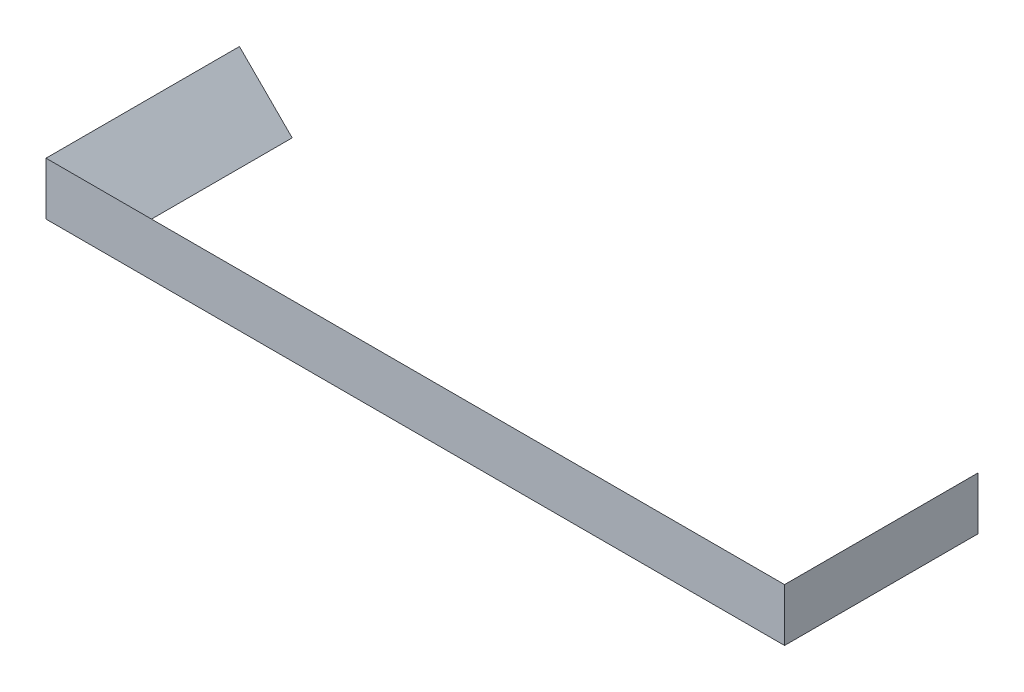
SolidWorks part; units mm, degrees
ref_plane "Спереди" through (0, 0, 0) normal (0, 0, 1) x (1, 0, 0)
ref_plane "Сверху" through (0, 0, 0) normal (0, 1, 0) x (1, 0, 0)
ref_plane "Слева" through (0, 0, 0) normal (1, 0, 0) x (0, 0, -1)
sketch "Эскиз1" plane through (0, 0, 0) normal (0, 1, 0) x (1, 0, 0)
  line L1 (0, 0) -> (84, 0) construction
  line L2 (0, 0) -> (0, -22)
  line L3 (0, -22) -> (84, -22)
  line L4 (84, 0) -> (84, -22)
  dimension "D1" = 22
  dimension "D2" = 84
sketch "Эскиз2" plane through (0, 0, 0) normal (0, 0, 1) x (1, 0, 0)
  line L0 (6, 0) -> (0, 0)
  line L1 (0, 0) -> (0, 6)
  line L2 (0, 6) -> (6, 0)
  line L3 (0, 0) -> (0, -9.1029) construction
  dimension "D1" = 6
sweep "По траектории1" add profiles "Эскиз2" path "Эскиз1"
